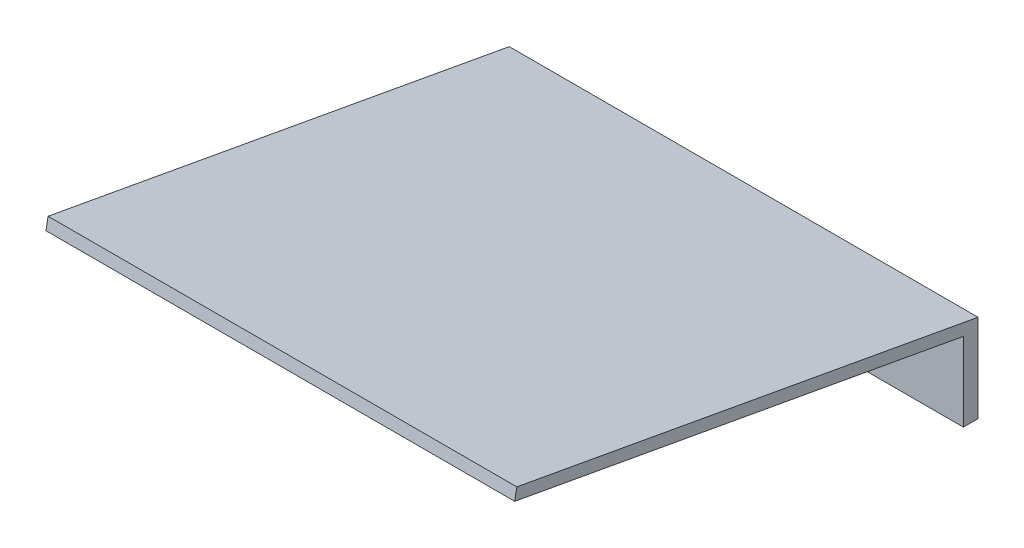
SolidWorks part; units mm, degrees
ref_plane "Plano frontal" through (0, 0, 0) normal (0, 0, 1) x (1, 0, 0)
ref_plane "Plano superior" through (0, 0, 0) normal (0, 1, 0) x (1, 0, 0)
ref_plane "Plano direito" through (0, 0, 0) normal (1, 0, 0) x (0, 0, -1)
ref_plane "Plano1" through (80, 0, 0) normal (1, 0, 0) x (0, 0, -1)
sketch "Esboço1" plane through (80, 0, 0) normal (1, 0, 0) x (0, 0, -1)
  line L0 (-2.5, 0) -> (0, 0)
  line L1 (0, 0) -> (0, 15)
  line L2 (0, 15) -> (-78.7143, 29.2852)
  line L3 (-78.7143, 29.2852) -> (-79.0714, 27.3173)
  line L4 (-79.0714, 27.3173) -> (-2.5, 13.421)
  line L5 (-2.5, 13.421) -> (-2.5, 0)
extrude "Ressalto-extrusão1" add sketch "Esboço1" against normal mid plane 80
